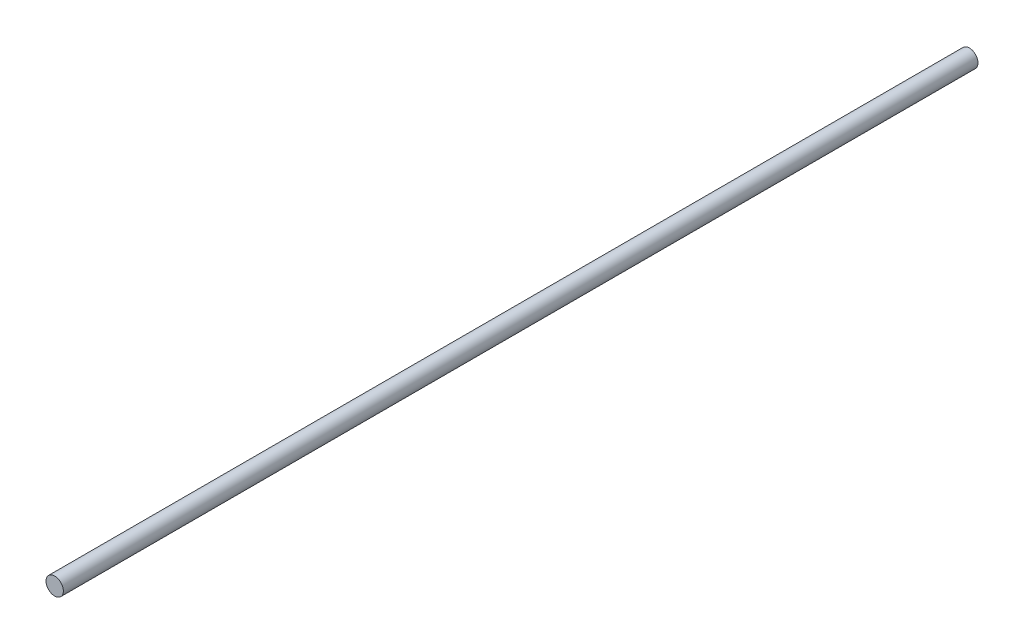
SolidWorks part; units mm, degrees
ref_plane "Front Plane" through (0, 0, 0) normal (0, 0, 1) x (1, 0, 0)
ref_plane "Top Plane" through (0, 0, 0) normal (0, 1, 0) x (1, 0, 0)
ref_plane "Right Plane" through (0, 0, 0) normal (1, 0, 0) x (0, 0, -1)
sketch "Sketch1" plane through (0, 0, 0) normal (0, 0, 1) x (1, 0, 0)
  circle A0 centre (0, 0) radius 19.05
  dimension "D1" = 38.1
extrude "Boss-Extrude1" add sketch "Sketch1" along normal blind 2006.6
